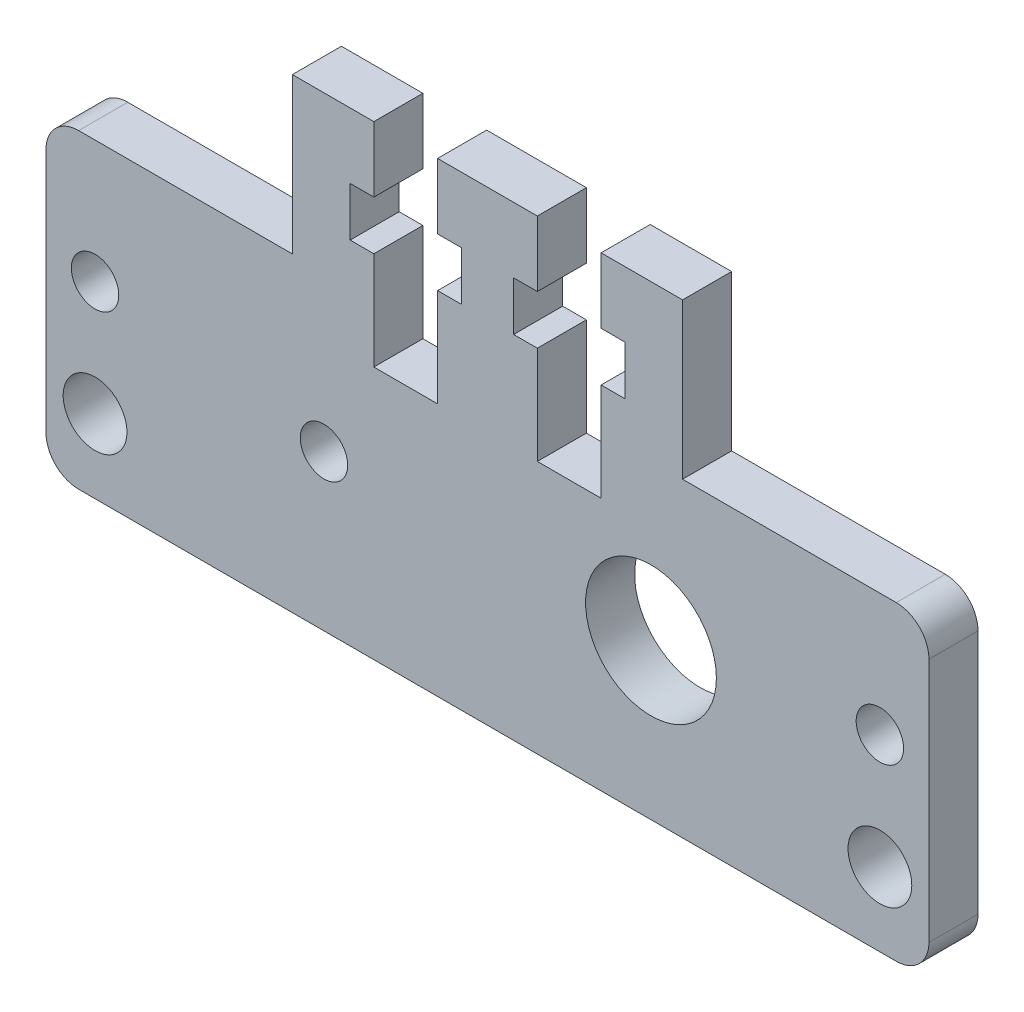
SolidWorks part; units mm, degrees
ref_plane "Front Plane" through (0, 0, 0) normal (0, 0, 1) x (1, 0, 0)
ref_plane "Top Plane" through (0, 0, 0) normal (0, 1, 0) x (1, 0, 0)
ref_plane "Right Plane" through (0, 0, 0) normal (1, 0, 0) x (0, 0, -1)
sketch "Sketch1" plane through (0, 0, -5.5516) normal (0, 0, 1) x (1, 0, 0)
  line L0 (-25.4646, 10.1373) -> (-12.3968, 10.1373)
  line L1 (-27.4646, 8.1373) -> (-27.4646, -6.8627)
  line L2 (26.5354, 8.1373) -> (26.5354, -6.8627)
  line L3 (-25.4646, -8.8627) -> (-10, -8.8627)
  line L4 (-20.7646, 10.1373) -> (-25.9646, 10.1373) construction
  line L5 (-20.7646, -8.8627) -> (-25.9646, -8.8627) construction
  line L6 (-27.4646, -2.971) -> (-27.4646, 4.2457) construction
  line L7 (-12.3968, 10.1373) -> (-12.3968, 19.6373)
  line L8 (-27.4646, 0.6373) -> (26.5354, 0.6373) construction
  line L9 (-24.4646, 10.1373) -> (-24.4646, -8.8627) construction
  line L10 (23.5354, 10.1373) -> (23.5354, -8.8627) construction
  line L27 (6.4854, 19.6373) -> (2.5854, 19.6373) construction
  line L28 (6.4854, 19.6373) -> (6.4854, 15.6373)
  line L40 (4.5354, 19.6373) -> (4.5354, 6.6373) construction
  line L41 (-10, -8.8627) -> (24.5354, -8.8627)
  line L42 (6.4854, 6.6373) -> (2.5854, 6.6373)
  line L44 (6.4854, 12.6373) -> (7.9354, 12.6373)
  line L46 (7.9354, 12.6373) -> (7.9354, 15.6373)
  line L47 (6.4854, 15.6373) -> (7.9354, 15.6373)
  line L48 (6.4854, 12.6373) -> (6.4854, 6.6373)
  line L49 (2.5854, 12.6373) -> (2.5854, 6.6373)
  line L50 (2.5854, 15.6373) -> (1.1354, 15.6373)
  line L51 (1.1354, 12.6373) -> (1.1354, 15.6373)
  line L52 (2.5854, 12.6373) -> (1.1354, 12.6373)
  line L53 (2.5854, 19.6373) -> (2.5854, 15.6373)
  line L54 (-3.5146, 19.6373) -> (-7.4146, 19.6373) construction
  line L55 (-3.5146, 19.6373) -> (-3.5146, 15.6373)
  line L56 (-5.4646, 19.6373) -> (-5.4646, 6.6373) construction
  line L57 (-3.5146, 6.6373) -> (-7.4146, 6.6373)
  line L58 (-3.5146, 12.6373) -> (-2.0646, 12.6373)
  line L59 (-2.0646, 12.6373) -> (-2.0646, 15.6373)
  line L60 (-3.5146, 15.6373) -> (-2.0646, 15.6373)
  line L61 (-3.5146, 12.6373) -> (-3.5146, 6.6373)
  line L62 (-7.4146, 12.6373) -> (-7.4146, 6.6373)
  line L63 (-7.4146, 15.6373) -> (-8.8646, 15.6373)
  line L64 (-8.8646, 12.6373) -> (-8.8646, 15.6373)
  line L65 (-7.4146, 12.6373) -> (-8.8646, 12.6373)
  line L66 (-7.4146, 19.6373) -> (-7.4146, 15.6373)
  line L70 (-0.4646, 80.7583) -> (-0.4646, -22.1769) construction
  line L71 (-12.3968, 19.6373) -> (-7.4146, 19.6373)
  line L73 (-3.5146, 19.6373) -> (2.5854, 19.6373)
  line L75 (6.4854, 19.6373) -> (11.4676, 19.6373)
  line L76 (11.4676, 19.6373) -> (11.4676, 10.1373)
  line L77 (11.4676, 10.1373) -> (24.5354, 10.1373)
  line L79 (26.5354, -7.3627) -> (26.5354, 8.6373) construction
  line L80 (25.0354, 10.1373) -> (19.5354, 10.1373) construction
  arc A0 (24.5354, 10.1373) -> (26.5354, 8.1373) centre (24.5354, 8.1373) cw
  arc A1 (26.5354, -6.8627) -> (24.5354, -8.8627) centre (24.5354, -6.8627) cw
  arc A2 (-27.4646, -6.8627) -> (-25.4646, -8.8627) centre (-25.4646, -6.8627) ccw
  arc A3 (-27.4646, 8.1373) -> (-25.4646, 10.1373) centre (-25.4646, 8.1373) cw
  circle A5 centre (-24.4646, -4.3627) radius 1.95
  circle A6 centre (23.5354, -4.3627) radius 1.95
  circle A12 centre (9.5354, 0.6373) radius 4
  circle A13 centre (-10.4646, 0.6373) radius 1.45
  circle A14 centre (-24.4646, 2.6373) radius 1.45
  circle A15 centre (23.5354, 2.6373) radius 1.45
  arc A16 (25.1969, -3.2494) -> (25.0665, -5.6494) centre (23.5354, -4.3627) ccw construction
  circle A17 centre (9.5354, 0.6373) radius 5 construction
  arc A19 (-25.9958, -5.6494) -> (-26.1261, -3.2494) centre (-24.4646, -4.3627) ccw construction
  point P73 (-0.4646, 80.7583)
  dimension "D1" = 2
  dimension "D2" = 8
  dimension "D3" = 2.9
  dimension "D4" = 2.9
  dimension "D5" = 2.9
  dimension "D19" = 2
  dimension "D20" = 3.9
  dimension "D21" = 27
  dimension "D22" = 3.9
  dimension "D6" = 3.9
  dimension "D7" = 4
  dimension "D8" = 6
  dimension "D9" = 3
  dimension "D10" = 1.45
  dimension "D11" = 3.9
  dimension "D12" = 4
  dimension "D13" = 6
  dimension "D14" = 3
  dimension "D15" = 1.45
  dimension "D16" = 10
  dimension "D17" = 6
  dimension "D18" = 20
  dimension "D23" = 2
extrude "Boss-Extrude1" add sketch "Sketch1" along normal blind 3
